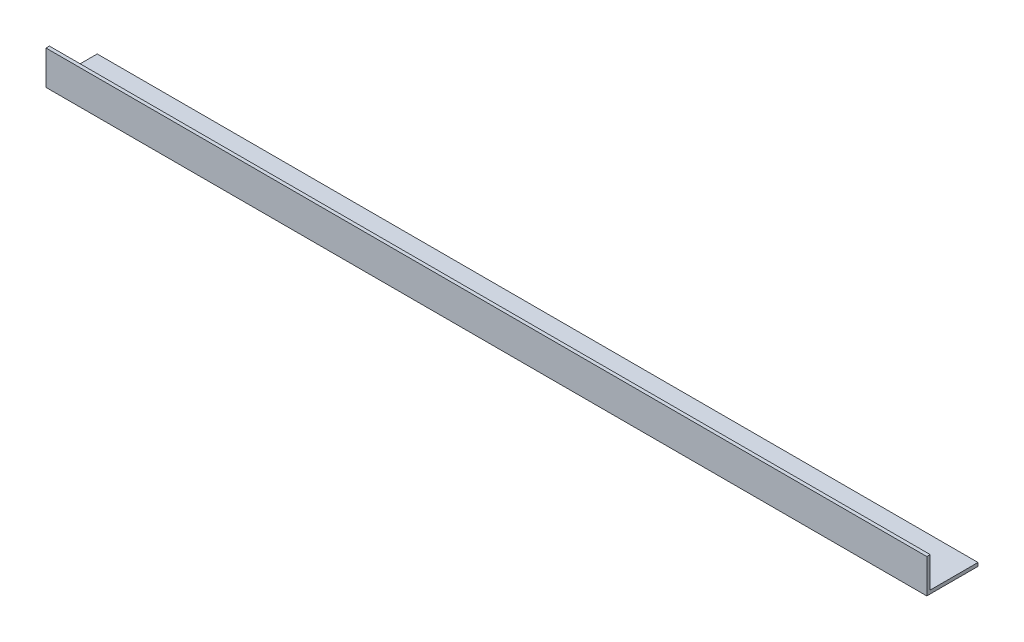
SolidWorks part; units mm, degrees
ref_plane "Alzado" through (0, 0, 0) normal (0, 0, 1) x (1, 0, 0)
ref_plane "Planta" through (0, 0, 0) normal (0, 1, 0) x (1, 0, 0)
ref_plane "Vista lateral" through (0, 0, 0) normal (1, 0, 0) x (0, 0, -1)
sketch "Croquis1" plane through (0, 0, 0) normal (1, 0, 0) x (0, 0, -1)
  line L0 (0, 10) -> (0, 0)
  line L1 (0, 0) -> (15, 0)
  line L2 (15, 0) -> (15, 1)
  line L3 (15, 1) -> (1, 1)
  line L4 (1, 1) -> (1, 10)
  line L5 (1, 10) -> (0, 10)
  dimension "D1" = 10
  dimension "D2" = 15
  dimension "D3" = 1
extrude "Saliente-Extruir1" add sketch "Croquis1" along normal blind 258
